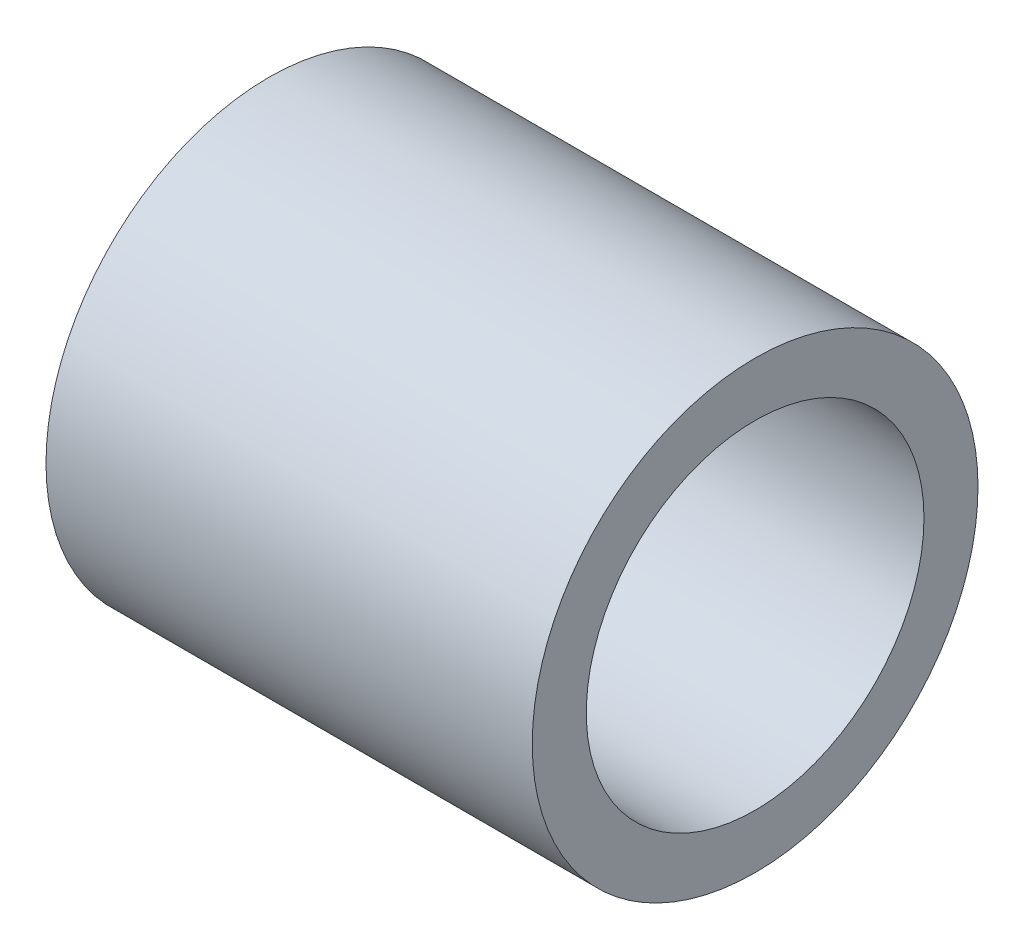
SolidWorks part; units mm, degrees
material "Aluminum Bronze"
ref_plane "Front Plane" through (0, 0, 0) normal (0, 0, 1) x (1, 0, 0)
ref_plane "Top Plane" through (0, 0, 0) normal (0, 1, 0) x (1, 0, 0)
ref_plane "Right Plane" through (0, 0, 0) normal (1, 0, 0) x (0, 0, -1)
sketch "Sketch1" plane through (0, 0, 0) normal (1, 0, 0) x (0, 0, -1)
  circle A0 centre (0, 0) radius 10.4775
  dimension "D1" = 20.955
extrude "Boss-Extrude1" add sketch "Sketch1" along normal blind 22.86
sketch "Sketch2" plane through (22.86, 0, 0) normal (1, 0, 0) x (0, 0, -1)
  point P0 (0, 0)
hole_wizard "#97 (0.625) Diameter Hole1" positions "Sketch2" profile "Sketch3" hole size "#97" standard "ANSI Inch" end condition through all
sketch "Sketch3" plane through (22.86, 0, 0) normal (0, 1, 0) x (0, 0, -1)
  line L0 (0, 0) -> (0, 22.86)
  line L1 (0, 22.86) -> (7.9375, 22.86)
  line L2 (7.9375, 22.86) -> (7.9375, 0)
  line L5 (7.9375, 0) -> (0, 0)
  line L11 (0, -6.35) -> (0, 107.95) construction
  dimension "Thru Hole Dia." = 15.875
  dimension "Thru Hole Depth" = 22.86
